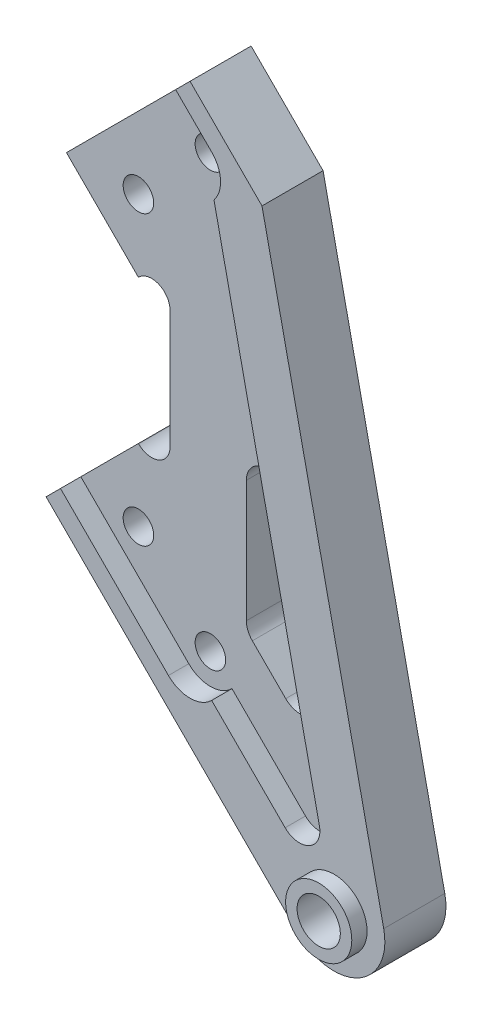
SolidWorks part; units mm, degrees
ref_plane "Front Plane" through (0, 0, 0) normal (0, 0, 1) x (1, 0, 0)
ref_plane "Top Plane" through (0, 0, 0) normal (0, 1, 0) x (1, 0, 0)
ref_plane "Right Plane" through (0, 0, 0) normal (1, 0, 0) x (0, 0, -1)
sketch "Sketch1" plane through (0, 0, 0) normal (0, 0, 1) x (1, 0, 0)
  line L0 (-15.2132, -28.2843) -> (-1.0711, -42.4264) construction
  line L1 (-15.2132, 28.2843) -> (-1.0711, 42.4264) construction
  line L2 (-15.2132, 14.1421) -> (-15.1716, 14.1838)
  line L3 (13.0711, 42.4264) -> (-1.0711, 56.5685)
  line L4 (-1.0711, 56.5685) -> (-29.3553, 28.2843)
  line L5 (-29.3553, 28.2843) -> (-15.2132, 14.1421)
  line L6 (-15.2132, -14.1421) -> (-15.1716, -14.1838)
  line L7 (13.0711, -42.4264) -> (-1.0711, -56.5685) construction
  line L8 (20.1421, -77.7817) -> (-29.3553, -28.2843)
  line L9 (-29.3553, -28.2843) -> (-15.2132, -14.1421)
  line L10 (-1.0711, 42.4264) -> (6, 49.4975) construction
  line L11 (-1.0711, -42.4264) -> (6, -49.4975) construction
  line L12 (0, 29.3553) -> (0, -29.3553) construction
  line L13 (-9, 11.6274) -> (-9, -11.6274)
  line L14 (6, -9.7985) -> (6, -33.6985)
  line L15 (7.1716, -36.5269) -> (13.7336, -43.0889)
  line L16 (20.4723, -39.4181) -> (13.9103, -8.9562)
  line L17 (-9, -20.3553) -> (9, -38.3553) construction
  line L18 (-9, 20.3553) -> (9, 38.3553) construction
  line L19 (-15.2132, -28.2843) -> (-22.2843, -21.2132) construction
  line L20 (-15.2132, 28.2843) -> (-22.2843, 21.2132) construction
  line L21 (36.989, -68.6048) -> (13.0711, 42.4264)
  circle A0 centre (-1.0711, 42.4264) radius 3
  circle A1 centre (-15.2132, 28.2843) radius 3
  circle A2 centre (-15.2132, -28.2843) radius 3
  circle A3 centre (-1.0711, -42.4264) radius 3
  arc A4 (13.7336, -43.0889) -> (20.4723, -39.4181) centre (16.562, -40.2605) ccw
  arc A5 (6, -33.6985) -> (7.1716, -36.5269) centre (10, -33.6985) ccw
  arc A6 (-9, 11.6274) -> (-15.1716, 14.1838) centre (-12.6152, 11.6274) ccw
  arc A7 (-9, -11.6274) -> (-15.1716, -14.1838) centre (-12.6152, -11.6274) cw
  circle A8 centre (27.2132, -70.7107) radius 4.25
  arc A9 (20.1421, -77.7817) -> (36.989, -68.6048) centre (27.2132, -70.7107) ccw
  arc A10 (6, -9.7985) -> (13.9103, -8.9562) centre (10, -9.7985) cw
  point P43 (6, -35.3553)
  dimension "D8" = 6
  dimension "D9" = 9
  dimension "D12" = 8.5
  dimension "D16" = 4
  dimension "D1" = 20
  dimension "D2" = 10
  dimension "D3" = 20
  dimension "D4" = 40
  dimension "D5" = 70
  dimension "D6" = 45
  dimension "D7" = 70
  dimension "D10" = 0.0589
  dimension "D11" = 70
  dimension "D13" = 0.0589
  dimension "D14" = 15
  dimension "D15" = 10
extrude "Boss-Extrude1" add sketch "Sketch1" along normal blind 8
sketch "Sketch2" plane through (0, 0, 8) normal (0, 0, 1) x (1, 0, 0)
  line L0 (20.4723, -39.4181) -> (13.9103, -8.9562) construction
  line L1 (36.989, -68.6048) -> (13.0711, 42.4264) construction
  line L2 (-29.3553, -28.2843) -> (20.1421, -77.7817) construction
  line L3 (13.0711, 42.4264) -> (-1.0711, 56.5685) construction
  line L4 (24.3552, -57.4431) -> (3.6416, 38.7129)
  line L5 (36.989, -68.6048) -> (13.0711, 42.4264)
  line L6 (-29.3553, -28.2843) -> (20.1421, -77.7817)
  line L7 (13.0711, 42.4264) -> (-1.0711, 56.5685)
  line L8 (17.6164, -61.1139) -> (3.1716, -46.669)
  line L9 (-29.3553, -28.2843) -> (-26.5269, -25.4558)
  line L10 (-15.2132, -14.1421) -> (-29.3553, -28.2843) construction
  line L11 (-26.5269, -25.4558) -> (-5.3137, -46.669)
  line L12 (3.1716, 46.669) -> (-3.8995, 53.7401)
  line L13 (-1.0711, 56.5685) -> (-29.3553, 28.2843) construction
  line L14 (-3.8995, 53.7401) -> (-1.0711, 56.5685)
  circle A0 centre (27.2132, -70.7107) radius 4.25 construction
  arc A1 (20.1421, -77.7817) -> (36.989, -68.6048) centre (27.2132, -70.7107) ccw construction
  circle A2 centre (27.2132, -70.7107) radius 4.25
  arc A3 (20.1421, -77.7817) -> (36.989, -68.6048) centre (27.2132, -70.7107) ccw
  arc A4 (-5.3137, -46.669) -> (3.1716, -46.669) centre (-1.0711, -42.4264) ccw
  arc A6 (3.6416, 38.7129) -> (3.1716, 46.669) centre (-1.0711, 42.4264) ccw
  arc A7 (24.3552, -57.4431) -> (17.6164, -61.1139) centre (20.4449, -58.2855) cw
  dimension "D1" = 12
  dimension "D3" = 4
  dimension "D2" = 10
extrude "Boss-Extrude2" add sketch "Sketch2" along normal blind 4
sketch "Sketch3" plane through (0, 0, 12) normal (0, 0, 1) x (1, 0, 0)
  circle A0 centre (27.2132, -70.7107) radius 6.5
  circle A1 centre (27.2132, -70.7107) radius 4.25 construction
  circle A2 centre (27.2132, -70.7107) radius 4.25
  dimension "D1" = 13
extrude "Boss-Extrude3" add sketch "Sketch3" along normal blind 3
